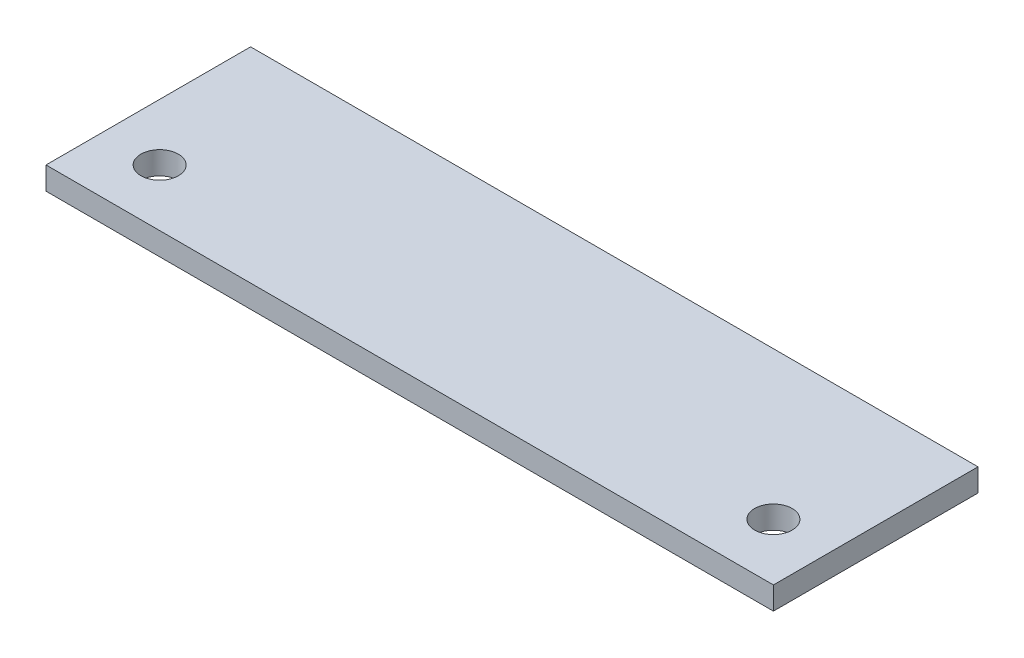
SolidWorks part; units mm, degrees
ref_plane "Front Plane" through (0, 0, 0) normal (0, 0, 1) x (1, 0, 0)
ref_plane "Top Plane" through (0, 0, 0) normal (0, 1, 0) x (1, 0, 0)
ref_plane "Right Plane" through (0, 0, 0) normal (1, 0, 0) x (0, 0, -1)
sketch "Sketch1" plane through (0, 0, 0) normal (0, 1, 0) x (1, 0, 0)
  line L1 (0, 0) -> (406.4, 0)
  line L2 (0, 0) -> (0, 114.3)
  line L3 (0, 114.3) -> (406.4, 114.3)
  line L4 (406.4, 0) -> (406.4, 114.3)
  dimension "D1" = 114.3
  dimension "D2" = 406.4
extrude "Boss-Extrude1" add sketch "Sketch1" along normal blind 12.7
sketch "Sketch2" plane through (0, 12.7, 0) normal (0, 1, 0) x (1, 0, 0)
  line L0 (0, 114.3) -> (0, 0) construction
  line L1 (0, 0) -> (406.4, 0) construction
  line L3 (203.2, 114.3) -> (203.2, 0) construction
  line L4 (406.4, 114.3) -> (0, 114.3) construction
  line L5 (0, 31.75) -> (406.4, 31.75) construction
  line L6 (406.4, 0) -> (406.4, 114.3) construction
  circle A0 centre (31.75, 31.75) radius 10.4775
  circle A1 centre (374.65, 31.75) radius 10.4775
  dimension "D1" = 31.75
  dimension "D3" = 20.955
  dimension "D2" = 31.75
extrude "Cut-Extrude1" cut sketch "Sketch2" against normal up to next
sketch3d "3DSketch1" plane through (0, 0, 0) normal (0, 0, 1) x (1, 0, 0)
  dimension "D1" = 152.4
